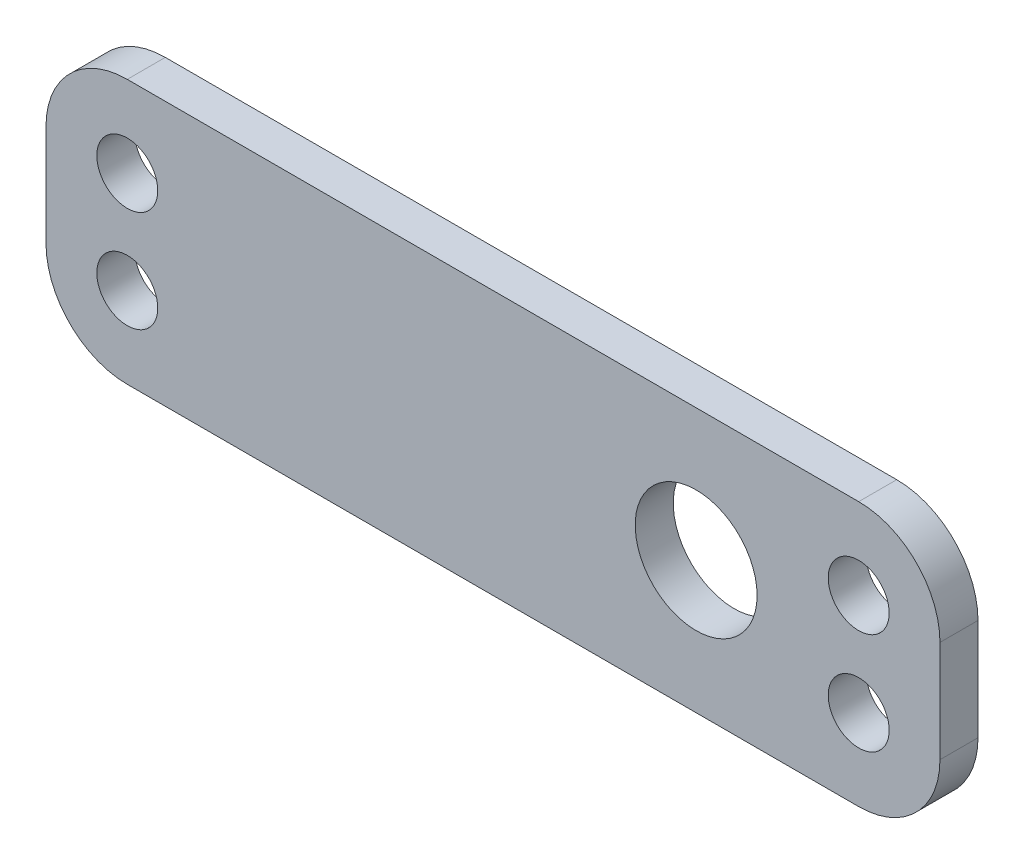
SolidWorks part; units mm, degrees
ref_plane "Front Plane" through (0, 0, 0) normal (0, 0, 1) x (1, 0, 0)
ref_plane "Top Plane" through (0, 0, 0) normal (0, 1, 0) x (1, 0, 0)
ref_plane "Right Plane" through (0, 0, 0) normal (1, 0, 0) x (0, 0, -1)
sketch "Sketch1" plane through (0, 0, 0) normal (0, 0, 1) x (1, 0, 0)
  line L1 (-34.925, 10.3187) -> (34.925, 10.3187)
  line L2 (-34.925, 10.3187) -> (-34.925, -10.3187)
  line L3 (-34.925, -10.3187) -> (34.925, -10.3187)
  line L4 (34.925, 10.3187) -> (34.925, -10.3187)
  circle A0 centre (-28.575, 3.9688) radius 2.3813
  circle A1 centre (-28.575, -3.9688) radius 2.3813
  circle A2 centre (28.575, 3.9688) radius 2.3812
  circle A3 centre (28.575, -3.9688) radius 2.3812
  point P18 (0, 10.3187)
  point P20 (34.925, 0)
  dimension "D2" = 4.7625
  dimension "D1" = 7.9375
  dimension "D3" = 57.15
  dimension "D4" = 6.35
  dimension "D5" = 6.35
  dimension "D6" = 6.35
  dimension "D7" = 6.35
extrude "Boss-Extrude1" add sketch "Sketch1" along normal blind 2.9718
fillet "Fillet1" radius 6.35 4 edges at (-34.925, -10.3187, 1.4859) (-34.925, 10.3187, 1.4859) (34.925, -10.3187, 1.4859) (34.925, 10.3187, 1.4859)
sketch "Sketch2" plane through (0, 0, 2.9718) normal (0, 0, 1) x (1, 0, 0)
  line L0 (34.925, -3.9688) -> (34.925, 3.9688) construction
  circle A0 centre (15.875, 0) radius 4.7625
  dimension "D2" = 9.525
  dimension "D1" = 19.05
extrude "Cut-Extrude1" cut sketch "Sketch2" against normal through all
